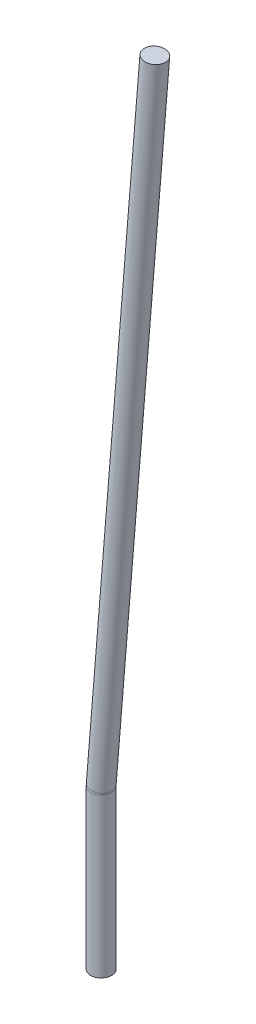
SolidWorks part; units mm, degrees
material "3.0517 (EN-AW 3003)"
ref_plane "Front" through (0, 0, 0) normal (0, 0, 1) x (1, 0, 0)
ref_plane "Top" through (0, 0, 0) normal (0, 1, 0) x (1, 0, 0)
ref_plane "Right" through (0, 0, 0) normal (1, 0, 0) x (0, 0, -1)
sketch "Sketch1" plane through (0, 0, 0) normal (0, 1, 0) x (1, 0, 0)
  circle A0 centre (0, 0) radius 0.2
  dimension "D1" = 0.4
extrude "Boss-Extrude1" add sketch "Sketch1" against normal blind 3
sketch "Sketch2" plane through (0, 0, 0) normal (0, 1, 0) x (1, 0, 0)
  line L0 (0.5, 0.2) -> (0.5, -0.2) construction
  circle A1 centre (0, 0) radius 0.2
  circle A2 centre (0, 0) radius 0.2
  point P5 (0.5, 0)
  dimension "D2" = 0.4
  dimension "D3" = 0.5
  dimension "D1" = 0
revolve "Revolve1" add sketch "Sketch2" angle 4.66 about L0
sketch "Sketch3" plane through (0.0033, 0.0405, 0) normal (0.0812, 0.9967, 0) x (0.9967, -0.0812, 0)
  circle A1 centre (-0.0017, 0) radius 0.2
  circle A2 centre (-0.0017, 0) radius 0.2
  dimension "D1" = 0
extrude "Boss-Extrude2" add sketch "Sketch3" along normal blind 12.5
